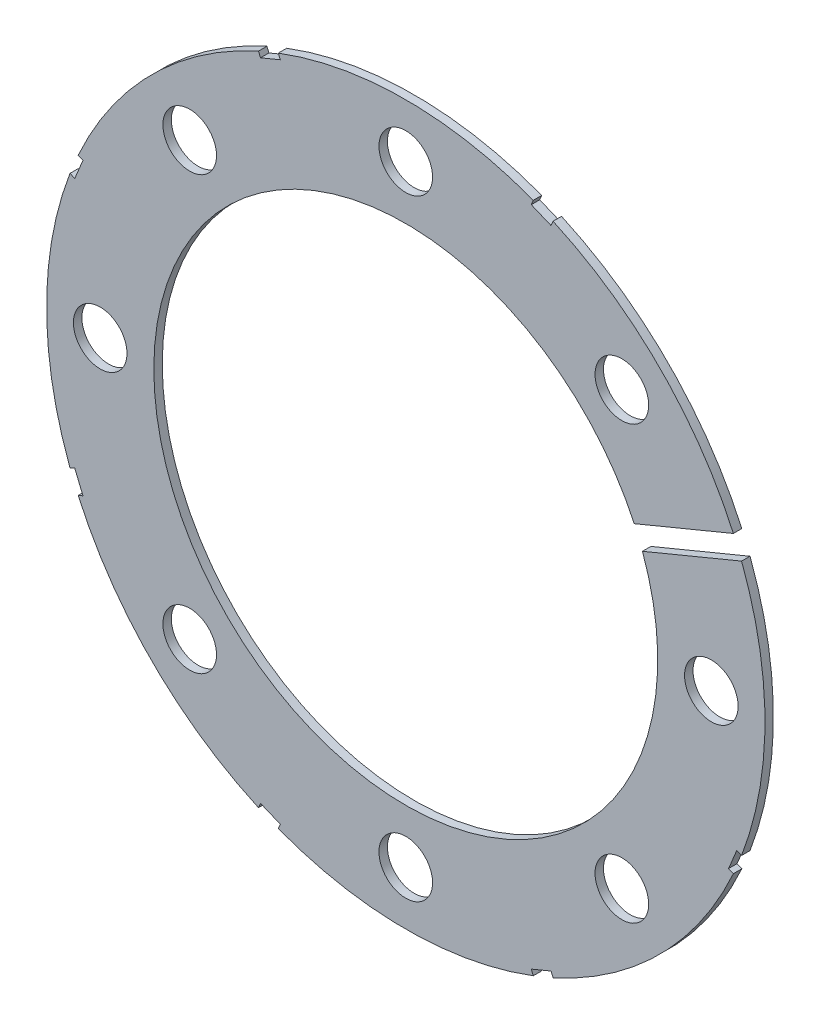
SolidWorks part; units mm, degrees
material "Copper"
ref_plane "Front Plane" through (0, 0, 0) normal (0, 0, 1) x (1, 0, 0)
ref_plane "Top Plane" through (0, 0, 0) normal (0, 1, 0) x (1, 0, 0)
ref_plane "Right Plane" through (0, 0, 0) normal (1, 0, 0) x (0, 0, -1)
sketch "Sketch4" plane through (0, 0, 0) normal (0, 0, 1) x (1, 0, 0)
  circle A0 centre (0, 0) radius 42.545
  dimension "D1" = 85.09
extrude "Boss-Extrude2" add sketch "Sketch4" along normal blind 1
sketch "Sketch5" plane through (0, 0, 1) normal (0, 0, 1) x (1, 0, 0)
  circle A0 centre (0, 0) radius 29.845
  circle A1 centre (0, 0) radius 42.545 construction
  dimension "D2" = 12.7
extrude "Cut-Extrude5" cut sketch "Sketch5" against normal through all
sketch "Sketch6" plane through (0, 0, 1) normal (0, 0, 1) x (1, 0, 0)
  circle A0 centre (36.195, 0) radius 3.175
  circle A4 centre (0, 0) radius 42.545 construction
  dimension "D2" = 6.35
  dimension "D1" = 6.35
extrude "Cut-Extrude6" cut sketch "Sketch6" against normal through all
pattern_circular "CirPattern1" count 8 over 360 about axis through (0, 0, 0) along (0, 0, 1) of "Cut-Extrude6"
sketch "Sketch8" plane through (0, 0, 1) normal (0, 0, 1) x (1, 0, 0)
  line L0 (42.3404, 18.9126) -> (23.5672, 11.1365)
  line L1 (42.3404, 18.9126) -> (43.3124, 16.566)
  line L2 (23.5672, 11.1365) -> (24.5392, 8.7898)
  line L3 (43.3124, 16.566) -> (24.5392, 8.7898)
  line L4 (42.3404, 18.9126) -> (24.5392, 8.7898) construction
  line L5 (23.5672, 11.1365) -> (43.3124, 16.566) construction
  line L6 (0, 0) -> (50.4438, 0) construction
  line L7 (17.6976, 39.4071) -> (15.3509, 40.3791)
  line L8 (17.6976, 39.4071) -> (17.2116, 38.2338)
  line L9 (15.3509, 40.3791) -> (14.8649, 39.2058)
  line L10 (17.2116, 38.2338) -> (14.8649, 39.2058)
  line L11 (15.3509, 40.3791) -> (17.2116, 38.2338) construction
  line L12 (17.6976, 39.4071) -> (14.8649, 39.2058) construction
  line L13 (-15.3509, 40.3791) -> (-17.6976, 39.4071)
  line L14 (-15.3509, 40.3791) -> (-14.8649, 39.2058)
  line L15 (-14.8649, 39.2058) -> (-17.2116, 38.2338)
  line L16 (-17.6976, 39.4071) -> (-17.2116, 38.2338)
  line L17 (-15.3509, 40.3791) -> (-17.2116, 38.2338) construction
  line L18 (-17.6976, 39.4071) -> (-14.8649, 39.2058) construction
  line L19 (-39.4071, 17.6976) -> (-40.3791, 15.3509)
  line L20 (-39.4071, 17.6976) -> (-38.2338, 17.2116)
  line L21 (-38.2338, 17.2116) -> (-39.2058, 14.8649)
  line L22 (-40.3791, 15.3509) -> (-39.2058, 14.8649)
  line L23 (-39.4071, 17.6976) -> (-39.2058, 14.8649) construction
  line L24 (-40.3791, 15.3509) -> (-38.2338, 17.2116) construction
  line L25 (-40.3791, -15.3509) -> (-39.4071, -17.6976)
  line L26 (-40.3791, -15.3509) -> (-39.2058, -14.8649)
  line L27 (-39.2058, -14.8649) -> (-38.2338, -17.2116)
  line L28 (-39.4071, -17.6976) -> (-38.2338, -17.2116)
  line L29 (-40.3791, -15.3509) -> (-38.2338, -17.2116) construction
  line L30 (-39.4071, -17.6976) -> (-39.2058, -14.8649) construction
  line L31 (-17.6976, -39.4071) -> (-15.3509, -40.3791)
  line L32 (-17.6976, -39.4071) -> (-17.2116, -38.2338)
  line L33 (-17.2116, -38.2338) -> (-14.8649, -39.2058)
  line L34 (-15.3509, -40.3791) -> (-14.8649, -39.2058)
  line L35 (-17.6976, -39.4071) -> (-14.8649, -39.2058) construction
  line L36 (-15.3509, -40.3791) -> (-17.2116, -38.2338) construction
  line L37 (15.3509, -40.3791) -> (17.6976, -39.4071)
  line L38 (15.3509, -40.3791) -> (14.8649, -39.2058)
  line L39 (14.8649, -39.2058) -> (17.2116, -38.2338)
  line L40 (17.6976, -39.4071) -> (17.2116, -38.2338)
  line L41 (15.3509, -40.3791) -> (17.2116, -38.2338) construction
  line L42 (17.6976, -39.4071) -> (14.8649, -39.2058) construction
  line L43 (39.4071, -17.6976) -> (40.3791, -15.3509)
  line L44 (39.4071, -17.6976) -> (38.2338, -17.2116)
  line L45 (38.2338, -17.2116) -> (39.2058, -14.8649)
  line L46 (40.3791, -15.3509) -> (39.2058, -14.8649)
  line L47 (39.4071, -17.6976) -> (39.2058, -14.8649) construction
  line L48 (40.3791, -15.3509) -> (38.2338, -17.2116) construction
  circle A0 centre (0, 0) radius 42.545 construction
  point P1 (33.4398, 13.8512)
  point P3 (16.2813, 39.3065)
  point P11 (-16.2813, 39.3065)
  point P20 (-39.3065, 16.2813)
  point P25 (-39.3065, -16.2813)
  point P26 (0, 0)
  point P31 (-16.2813, -39.3065)
  point P36 (16.2813, -39.3065)
  point P41 (39.3065, -16.2813)
  point P46 (0, 0)
  dimension "D1" = 20.32
  dimension "D2" = 6.35
  dimension "D3" = 2.54
  dimension "D4" = 22.5
  dimension "D5" = 1.27
  dimension "D6" = 2.54
  dimension "D7" = 1.27
  dimension "D8" = 1.27
  dimension "D9" = 0.635
  dimension "D10" = 67.5
  dimension "D12" = 0.635
  dimension "D11" = 7
extrude "Cut-Extrude11" cut sketch "Sketch8" against normal through all
